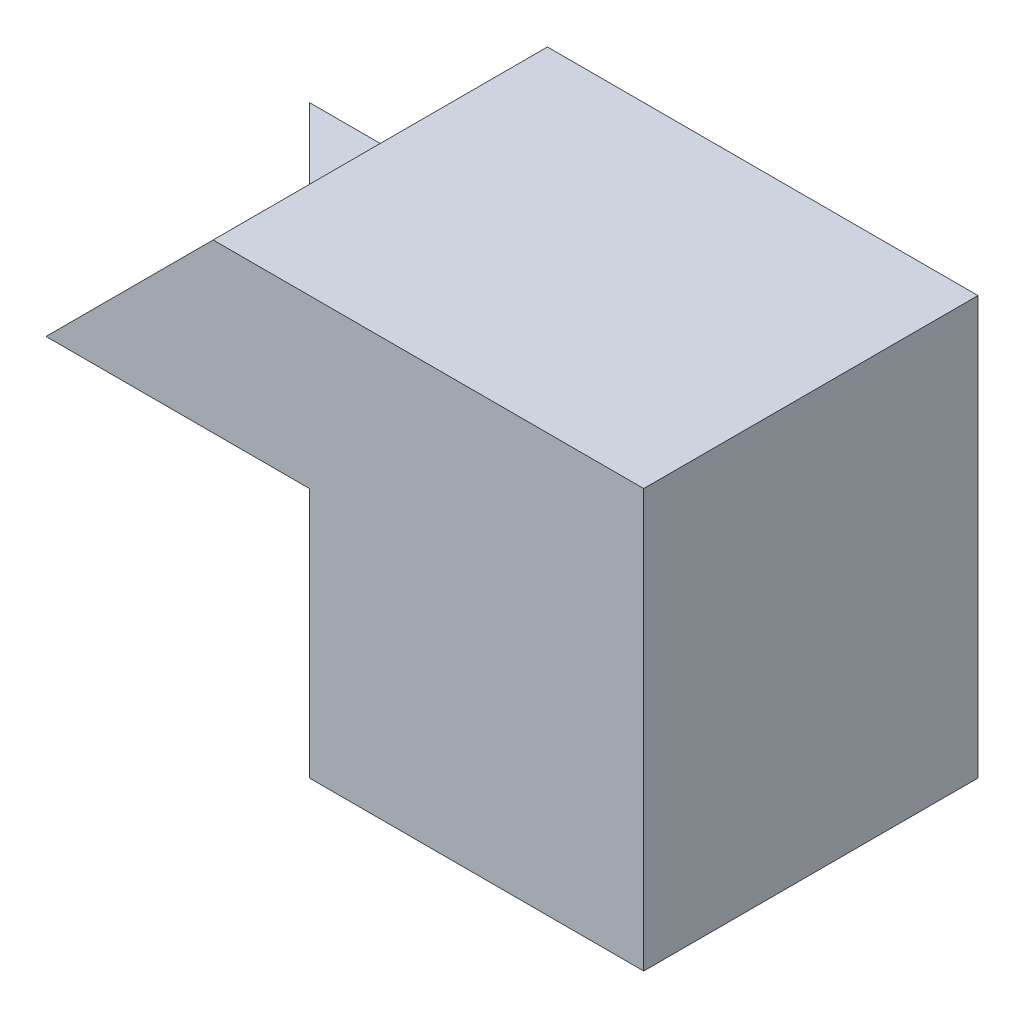
SolidWorks part; units mm, degrees
ref_plane "Front Plane" through (0, 0, 0) normal (0, 0, 1) x (1, 0, 0)
ref_plane "Top Plane" through (0, 0, 0) normal (0, 1, 0) x (1, 0, 0)
ref_plane "Right Plane" through (0, 0, 0) normal (1, 0, 0) x (0, 0, -1)
sketch "Sketch1" plane through (0, 0, 0) normal (0, 1, 0) x (1, 0, 0)
  line L0 (0, 0) -> (-4, 4)
  line L1 (-4, 4) -> (0, 4)
  line L2 (0, 4) -> (0, 0)
  dimension "D1" = 4
  dimension "D2" = 4
extrude "Boss-Extrude1" add sketch "Sketch1" along normal blind 3
sketch "Sketch2" plane through (0, 0, -4) normal (0, 0, -1) x (-1, 0, 0)
  line L0 (1.1523, 5) -> (3.1523, 3)
  line L1 (-4, 0) -> (-4, 5)
  line L2 (-4, 5) -> (1.1523, 5)
  line L3 (-4, 0) -> (0, 0)
  line L4 (0, 3) -> (4, 3) construction
  line L5 (0, 0) -> (0, 3)
  line L6 (0, 3) -> (3.1523, 3)
  dimension "D1" = 5
  dimension "D2" = 2
  dimension "D3" = 4
  dimension "D4" = 2
extrude "Boss-Extrude2" add sketch "Sketch2" against normal blind 4
